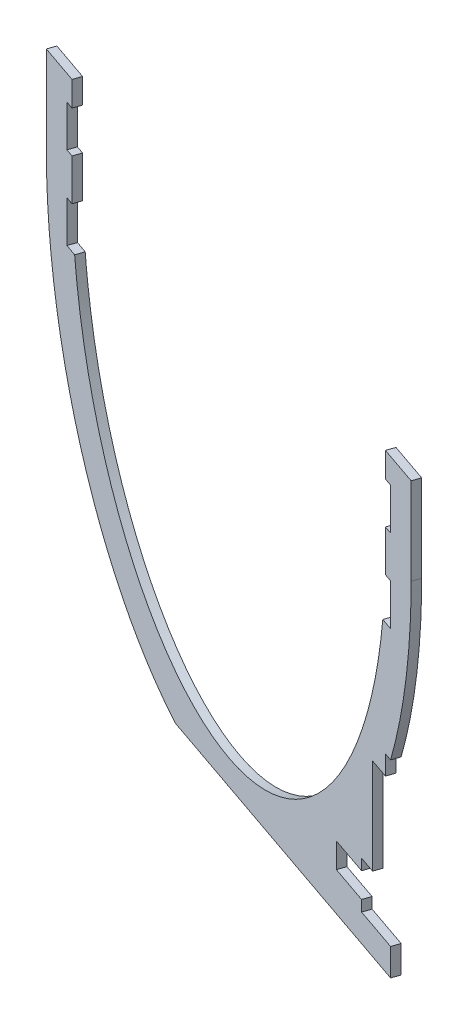
SolidWorks part; units mm, degrees
ref_plane "Front Plane" through (0, 0, 0) normal (0, 0, 1) x (1, 0, 0)
ref_plane "Top Plane" through (0, 0, 0) normal (0, 1, 0) x (1, 0, 0)
ref_plane "Right Plane" through (0, 0, 0) normal (1, 0, 0) x (0, 0, -1)
sketch "Sketch2" plane through (0, 0, 0) normal (0, 1, 0) x (1, 0, 0)
  line L0 (-295.0403, 95.1378) -> (-34.5174, 903.069) construction
  line L1 (-25, 910) -> (25, 910) construction
  line L2 (0, 0) -> (0, 870) construction
  line L3 (-181.6808, 251.1814) -> (-9.5174, 785.0928) construction
  line L4 (295.0403, 95.1378) -> (32.2825, 910) construction
  line L5 (181.6808, 251.1814) -> (9.5174, 785.0928) construction
  line L6 (-250, 0) -> (-250, 956.0819)
  line L7 (-250, 956.0819) -> (250, 783.9181)
  line L8 (-591.5307, 0) -> (570.3863, 0) construction
  line L9 (181.6808, -251.1814) -> (9.5174, -785.0928) construction
  line L10 (295.0403, -95.1378) -> (32.2825, -910) construction
  line L11 (-181.6808, -251.1814) -> (-9.5174, -785.0928) construction
  line L12 (-25, -910) -> (25, -910) construction
  line L13 (-295.0403, -95.1378) -> (-34.5174, -903.069) construction
  line L14 (250, 783.9181) -> (250, 0)
  line L15 (0, 870) -> (-535.6255, 184.4306)
  line L16 (250, 783.9181) -> (-338.6228, 30.5153)
  line L17 (-662.1318, 870) -> (570.3863, 870) construction
  line L18 (-338.6228, 30.5153) -> (-732.6282, 338.346)
  line L19 (-732.6282, 338.346) -> (-250, 956.0819)
  line L20 (0, 870) -> (-283.2443, 47.3988) construction
  circle A0 centre (0, 0) radius 250 construction
  arc A1 (181.6808, 251.1814) -> (-181.6808, 251.1814) centre (0, 0) ccw construction
  arc A2 (-9.5174, 785.0928) -> (9.5174, 785.0928) centre (0, 782.0238) cw construction
  arc A3 (-295.0403, 95.1378) -> (-295.0403, -95.1378) centre (0, 0) ccw construction
  arc A4 (-25, 910) -> (-34.5174, 903.069) centre (-25, 900) ccw construction
  arc A5 (25, 910) -> (34.5174, 903.069) centre (25, 900) cw construction
  arc A6 (0, 0) -> (-535.6255, 184.4306) centre (0, 870) cw construction
  arc A22 (25, -910) -> (34.5174, -903.069) centre (25, -900) ccw construction
  arc A23 (-25, -910) -> (-34.5174, -903.069) centre (-25, -900) cw construction
  arc A24 (-9.5174, -785.0928) -> (9.5174, -785.0928) centre (0, -782.0238) ccw construction
  arc A25 (181.6808, -251.1814) -> (-181.6808, -251.1814) centre (0, 0) cw construction
  arc A26 (-181.6808, -251.1814) -> (181.6808, -251.1814) centre (0, 0) ccw construction
  arc A27 (295.0403, -95.1378) -> (295.0403, 95.1378) centre (0, 0) ccw construction
  point P15 (0, 814.6081)
  point P17 (-32.2825, 910)
  point P21 (0, 910)
  point P69 (0, -910)
  dimension "D1" = 500
  dimension "D2" = 10
  dimension "D3" = 10
  dimension "D4" = 870
  dimension "D5" = 19
  dimension "D8" = 60
  dimension "D9" = 910
  dimension "D11" = 50
ref_plane "Plane1" through (0, 0, -870) normal (0, 0, 1) x (1, 0, 0)
sketch "Sketch3" plane through (0, 0, -870) normal (0, 0, 1) x (1, 0, 0)
  line L0 (0, 0) -> (0, 621.6859) construction
ref_plane "Plane2" through (267.8127, 0, -777.7847) normal (-0.3256, 0, 0.9455) x (0.9455, 0, 0.3256)
ref_plane "Plane3" through (261.3014, 0, -758.8743) normal (-0.3256, 0, 0.9455) x (0.9455, 0, 0.3256)
sketch "Sketch4" plane through (261.3014, 0, -758.8743) normal (-0.3256, 0, 0.9455) x (0.9455, 0, 0.3256)
  line L0 (-283.2443, 938.347) -> (-283.2443, -30) construction
  line L1 (-761.4579, 410) -> (151.8347, 410) construction
  line L2 (-538.2443, 410) -> (-538.2443, 470) construction
  line L3 (-538.2443, 470) -> (-558.2443, 470) construction
  line L4 (-558.2443, 470) -> (-558.2443, 350) construction
  line L5 (-558.2443, 470) -> (-544.8659, 527.0811) construction
  line L6 (-8.2443, 350) -> (-21.6227, 292.9189) construction
  line L7 (-558.2443, 350) -> (-544.8659, 292.9189) construction
  line L8 (-8.2443, 470) -> (-21.6227, 527.0811) construction
  line L9 (-8.2443, 470) -> (-8.2443, 350) construction
  line L10 (21.7557, 485) -> (21.7557, 515)
  line L11 (-386.784, -30) -> (-179.7046, -30)
  line L12 (21.7557, 515) -> (71.7557, 515)
  line L13 (-118.2838, 31.1787) -> (39.5332, 31.1787) construction
  line L14 (1.7557, 41.1787) -> (-13.2443, 41.1787) construction
  line L15 (-13.2443, 41.1787) -> (-13.2443, 31.1787) construction
  line L16 (6.7557, 35.1787) -> (26.7557, 35.1787) construction
  line L17 (26.7557, 35.1787) -> (26.7557, 31.1787) construction
  line L18 (1.7557, 48.6787) -> (6.7557, 48.6787) construction
  line L19 (-179.7046, -30) -> (31.7557, -30)
  line L20 (-3.2443, 119.3787) -> (-24.7443, 119.3787) construction
  line L21 (21.7557, 335) -> (31.7557, 335)
  line L22 (31.7557, 335) -> (31.7557, 485) construction
  line L23 (31.7557, 485) -> (21.7557, 485)
  line L24 (21.7557, 485) -> (21.7557, 335) construction
  line L25 (-3.2443, 119.3787) -> (-3.2443, -25) construction
  line L26 (71.7557, 515) -> (71.7557, 410)
  line L27 (21.7557, 515) -> (21.7557, 485)
  line L28 (-8.2443, 470) -> (1.7557, 470) construction
  line L29 (1.7557, 470) -> (1.7557, 350) construction
  line L30 (1.7557, 350) -> (-8.2443, 350) construction
  line L31 (1.7557, 470) -> (1.7557, 485) construction
  line L32 (1.7557, 485) -> (6.7557, 485) construction
  line L33 (6.7557, 485) -> (6.7557, 13.6787) construction
  line L34 (1.7557, 350) -> (1.7557, 13.6787) construction
  line L35 (1.7557, 13.6787) -> (6.7557, 13.6787) construction
  line L37 (-24.7443, 119.3787) -> (-24.7443, -25) construction
  line L38 (31.7557, -30) -> (31.7557, 2.9787)
  line L45 (-24.7443, 2.9787) -> (-3.2443, 2.9787)
  line L46 (-24.7443, 59.3787) -> (-3.2443, 59.3787)
  line L47 (-3.2443, 59.3787) -> (-3.2443, 127.2211)
  line L48 (-24.7443, 59.3787) -> (-24.7443, 2.9787)
  line L49 (-3.2443, 2.9787) -> (-3.2443, -25) construction
  line L54 (31.7557, 435) -> (21.7557, 435)
  line L55 (31.7557, 385) -> (21.7557, 385)
  line L56 (31.7557, 435) -> (31.7557, 485)
  line L57 (21.7557, 435) -> (21.7557, 385)
  line L58 (31.7557, 385) -> (31.7557, 335)
  line L59 (21.7557, 335) -> (16.6093, 335)
  line L60 (-638.2443, 515) -> (-638.2443, 410)
  line L61 (-588.2443, 515) -> (-638.2443, 515)
  line L62 (-598.2443, 485) -> (-588.2443, 485)
  line L63 (-598.2443, 435) -> (-598.2443, 485)
  line L64 (-598.2443, 435) -> (-588.2443, 435)
  line L65 (-598.2443, 385) -> (-588.2443, 385)
  line L66 (-588.2443, 435) -> (-588.2443, 385)
  line L67 (-598.2443, 385) -> (-598.2443, 335)
  line L68 (-588.2443, 335) -> (-583.0979, 335)
  line L69 (-588.2443, 335) -> (-598.2443, 335)
  line L70 (-588.2443, 485) -> (-588.2443, 515)
  line L71 (-19.7443, 59.3787) -> (-19.7443, 2.9787) construction
  line L72 (-24.7443, 46.1787) -> (-73.7443, 46.1787)
  line L73 (-73.7443, 46.1787) -> (-73.7443, 16.1787)
  line L74 (-24.7443, 16.1787) -> (-73.7443, 16.1787)
  line L75 (-3.2443, 2.9787) -> (21.7557, 2.9787)
  line L76 (21.7557, 174.6108) -> (21.7557, 2.9787) construction
  line L77 (31.7557, 2.9787) -> (31.7557, 197.8725) construction
  line L79 (-3.2443, 127.2211) -> (-3.2443, 174.6108)
  line L80 (-3.2443, 174.6108) -> (21.7557, 174.6108)
  line L81 (21.7557, 174.6108) -> (21.7557, 197.8725)
  line L82 (21.7557, 197.8725) -> (31.7557, 197.8725)
  line L83 (21.7557, 2.9787) -> (31.7557, 2.9787)
  ellipse E0 centre (-283.2443, 410) end of major axis (-283.2443, 55) minor radius 250 construction
  ellipse E1 centre (-283.2443, 410) end of major axis (-283.2443, 790) minor radius 275 construction
  ellipse E2 centre (-283.2443, 410) end of major axis (-283.2443, 788.3034) minor radius 275.1297 (-544.8659, 527.0811) -> (-21.6227, 527.0811) cw construction
  ellipse E3 centre (-283.2443, 410) end of major axis (-283.2443, 31.6966) minor radius 275.1297 (-544.8659, 292.9189) -> (-21.6227, 292.9189) ccw construction
  ellipse E4 centre (-283.2443, 410) end of major axis (-283.2443, 0) minor radius 305 (-588.2443, 410) -> (21.7557, 410) ccw construction
  ellipse E5 centre (-283.2443, 410) end of major axis (-283.2443, 870) minor radius 355 (-638.2443, 410) -> (-386.784, -30) ccw
  ellipse E6 centre (-283.2443, 410) end of major axis (-283.2443, -25) minor radius 332.1412 (48.8969, 410) -> (-283.2443, -25) cw construction
  ellipse E9 centre (-283.2443, 410) end of major axis (-283.2443, 0) minor radius 305 (16.6093, 335) -> (-583.0979, 335) cw
  ellipse E10 centre (-283.2443, 410) end of major axis (-283.2443, 870) minor radius 355 (31.7557, 197.8725) -> (71.7557, 410) ccw
  point P26 (-8.2443, 410)
  point P31 (-558.2443, 410)
  point P133 (-73.7443, 31.1787)
  dimension "D1" = 500
  dimension "D2" = 710
  dimension "D3" = 550
  dimension "D4" = 760
  dimension "D5" = 20
  dimension "D6" = 60
  dimension "D7" = 30
  dimension "D8" = 30
  dimension "D9" = 30
  dimension "D10" = 35
  dimension "D11" = 50
  dimension "D12" = 50
  dimension "D13" = 17.5
  dimension "D14" = 10
  dimension "D16" = 10
  dimension "D17" = 150
  dimension "D18" = 75
  dimension "D19" = 25
  dimension "D20" = 10
  dimension "D21" = 5
  dimension "D25" = 280
  dimension "D28" = 60
  dimension "D29" = 56.4
  dimension "D30" = 25
  dimension "D31" = 105
  dimension "D32" = 28.2
  dimension "D33" = 15
  dimension "D34" = 20
  dimension "D35" = 4
  dimension "D36" = 21.5
  dimension "D37" = 5
  dimension "D38" = 54
  dimension "D39" = 30
extrude "Boss-Extrude1" add sketch "Sketch4" along normal blind 10
